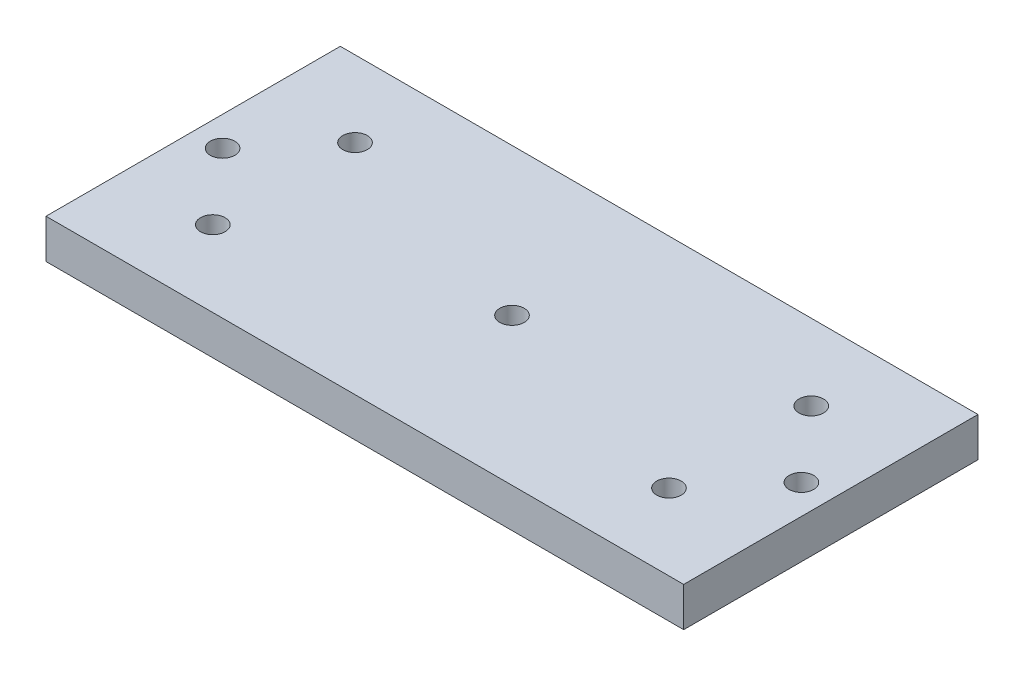
SolidWorks part; units mm, degrees
ref_plane "正面" through (0, 0, 0) normal (0, 0, 1) x (1, 0, 0)
ref_plane "平面" through (0, 0, 0) normal (0, 1, 0) x (1, 0, 0)
ref_plane "右側面" through (0, 0, 0) normal (1, 0, 0) x (0, 0, -1)
sketch "ｽｹｯﾁ1" plane through (0, 0, 0) normal (0, 1, 0) x (1, 0, 0)
  line L1 (-65, 30) -> (65, 30)
  line L2 (-65, 30) -> (-65, -30)
  line L3 (-65, -30) -> (65, -30)
  line L4 (65, 30) -> (65, -30)
  line L5 (-65, 30) -> (65, -30) construction
  line L6 (-65, -30) -> (65, 30) construction
  point P0 (0, 0)
  dimension "D1" = 60
  dimension "D2" = 130
extrude "ﾎﾞｽ - 押し出し1" add sketch "ｽｹｯﾁ1" along normal blind 8
sketch "ｽｹｯﾁ2" plane through (0, 8, 0) normal (0, 1, 0) x (1, 0, 0)
  line L0 (0, 0) -> (59, 0) construction
  line L1 (0, 0) -> (46.5, 0) construction
  line L2 (46.5, 0) -> (46.5, -14.5) construction
  line L3 (0, 0) -> (0, 30) construction
  line L4 (65, 30) -> (-65, 30) construction
  circle A0 centre (0, 0) radius 2.5
  circle A1 centre (59, 0) radius 2.5
  circle A2 centre (46.5, -14.5) radius 2.5
  circle A3 centre (46.5, 14.5) radius 2.5
  circle A4 centre (-46.5, -14.5) radius 2.5
  circle A5 centre (-59, 0) radius 2.5
  circle A6 centre (-46.5, 14.5) radius 2.5
extrude "ｶｯﾄ - 押し出し1" cut sketch "ｽｹｯﾁ2" against normal through all
